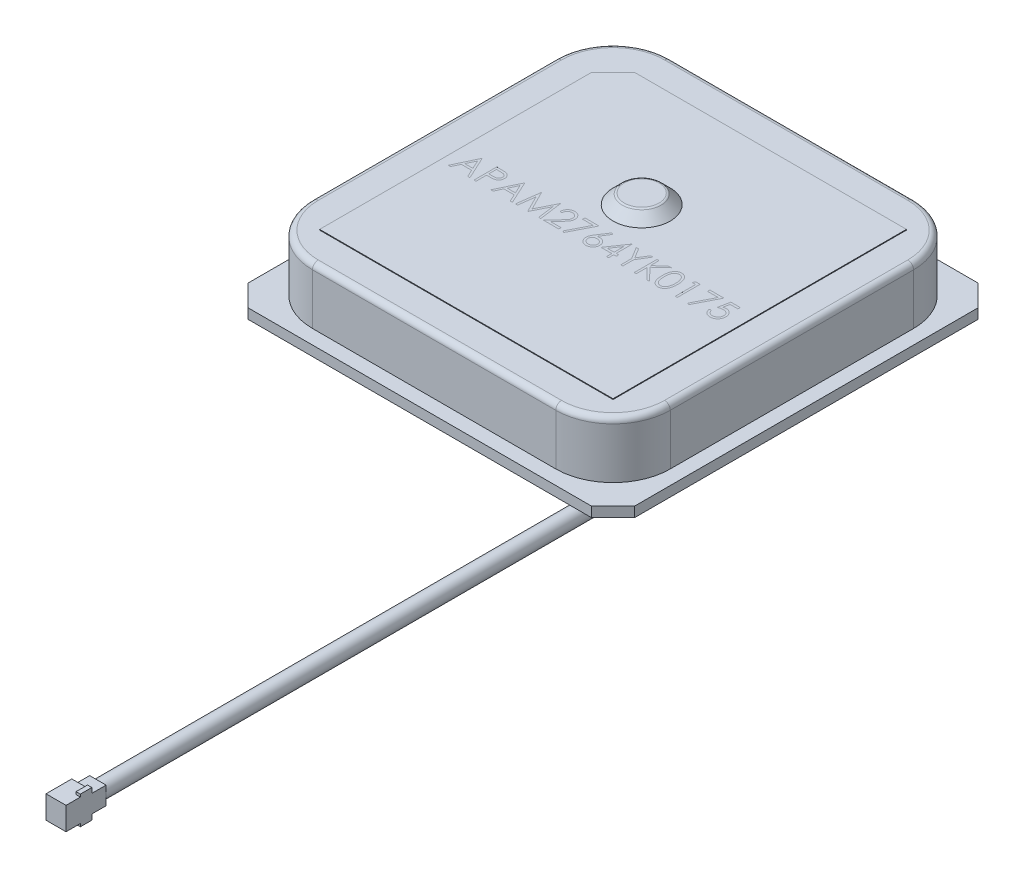
SolidWorks part; units mm, degrees
ref_plane "Front Plane" through (0, 0, 0) normal (0, 0, 1) x (1, 0, 0)
ref_plane "Top Plane" through (0, 0, 0) normal (0, 1, 0) x (1, 0, 0)
ref_plane "Right Plane" through (0, 0, 0) normal (1, 0, 0) x (0, 0, -1)
sketch "Sketch1" plane through (0, 0, 0) normal (0, 1, 0) x (1, 0, 0)
  line L0 (-13.5, -13.5) -> (13.5, -13.5)
  line L1 (-13.5, -13.5) -> (-13.5, 13.5)
  line L2 (13.5, -13.5) -> (13.5, 13.5)
  line L3 (-13.5, 13.5) -> (13.5, 13.5)
  line L4 (-13.5, -13.5) -> (13.5, 13.5) construction
  line L5 (13.5, -13.5) -> (-13.5, 13.5) construction
  point P1 (0, 0)
  dimension "D1" = 27
  dimension "D2" = 27
extrude "Boss-Extrude1" add sketch "Sketch1" along normal blind 0.7
chamfer "Chamfer2" distance 1.5 angle 45 4 edges at (-13.5, 0.35, 13.5) (13.5, 0.35, 13.5) (13.5, 0.35, -13.5) (-13.5, 0.35, -13.5)
sketch "Sketch2" plane through (0, 0.7, 0) normal (0, 1, 0) x (1, 0, 0)
  line L0 (-12.5, -12.5) -> (12.5, -12.5)
  line L1 (-12.5, -12.5) -> (-12.5, 12.5)
  line L2 (12.5, -12.5) -> (12.5, 12.5)
  line L3 (-12.5, 12.5) -> (12.5, 12.5)
  line L4 (-12.5, -12.5) -> (12.5, 12.5) construction
  line L5 (12.5, -12.5) -> (-12.5, 12.5) construction
  point P1 (0, 0)
  dimension "D1" = 25
  dimension "D2" = 25
extrude "Boss-Extrude3" add sketch "Sketch2" along normal blind 3.95 separate body
fillet "Fillet3" radius 4 4 edges at (12.5, 2.675, -12.5) (12.5, 2.675, 12.5) (-12.5, 2.675, 12.5) (-12.5, 2.675, -12.5)
sketch "Sketch3" plane through (0, 0, 0) normal (0, -1, 0) x (-1, 0, 0)
  line L0 (-11.5, -1.5) -> (3.5, -1.5)
  line L1 (-11.5, -1.5) -> (-11.5, 9.5)
  line L2 (3.5, -1.5) -> (3.5, 9.5)
  line L3 (-11.5, 9.5) -> (3.5, 9.5)
  line L5 (-13.5, -12) -> (-13.5, 12) construction
  line L6 (-12, 13.5) -> (12, 13.5) construction
  dimension "D1" = 15
  dimension "D2" = 11
  dimension "D3" = 15
  dimension "D4" = 17
fillet "Fillet4" radius 0.4 8 edges at (11.3284, 4.65, 11.3284) (0, 4.65, 12.5) (-11.3284, 4.65, 11.3284) (-12.5, 4.65, 0) (-11.3284, 4.65, -11.3284) (0, 4.65, -12.5) (11.3284, 4.65, -11.3284) (12.5, 4.65, 0)
sketch "Sketch5" plane through (0, 4.65, 0) normal (0, 1, 0) x (1, 0, 0)
  line L0 (-10.25, -10.25) -> (10.25, -10.25)
  line L1 (-10.25, -10.25) -> (-10.25, 10.25)
  line L2 (10.25, -10.25) -> (10.25, 10.25)
  line L3 (-10.25, 10.25) -> (10.25, 10.25)
  line L4 (-10.25, -10.25) -> (10.25, 10.25) construction
  line L5 (10.25, -10.25) -> (-10.25, 10.25) construction
  point P1 (0, 0)
  dimension "D1" = 20.5
  dimension "D2" = 20.5
extrude "Boss-Extrude6" add sketch "Sketch5" along normal blind 0.05
chamfer "Chamfer1" distance 1.5 angle 45 1 edges at (-10.25, 4.675, -10.25)
sketch "Sketch4" plane through (0, 4.7, 0) normal (0, 1, 0) x (1, 0, 0)
  line L1 (13.5, -12) -> (13.5, 12) construction
  line L2 (12, 13.5) -> (-12, 13.5) construction
  circle A0 centre (-0.5, 2.5) radius 2
  dimension "D1" = 4
  dimension "D2" = 14
  dimension "D3" = 11
extrude "Boss-Extrude5" add sketch "Sketch4" along normal blind 0.7 draft 45
fillet "Fillet1" radius 0.2 1 edges at (-0.5, 5.4, -1.2)
extrude "Boss-Extrude4" add sketch "Sketch3" along normal blind 1.3
sketch "Sketch6" plane through (0, 0, 1.5) normal (0, 0, 1) x (1, 0, 0)
  line L1 (11.5, -1.3) -> (11.5, 0) construction
  line L2 (14.85, 0) -> (-14.85, 0) construction
  circle A0 centre (10.7, -0.565) radius 0.565
  dimension "D3" = 1.13
  dimension "D2" = 0.8
extrude "Boss-Extrude10" add sketch "Sketch6" along normal blind 48 separate body
ref_plane "Plane1" through (11.28, 0, 0) normal (1, 0, 0) x (0, 0, -1)
sketch "Sketch7" plane through (11.28, 0, 0) normal (1, 0, 0) x (0, 0, -1)
  line L1 (-49.5, 0.235) -> (-47.7, 0.235)
  line L2 (-49.5, 0.235) -> (-49.5, -1.365)
  line L3 (-49.5, -1.365) -> (-47.7, -1.365)
  line L4 (-47.7, 0.235) -> (-47.7, -1.365)
  line L6 (-1.5, -0.565) -> (-17.1255, -0.565) construction
  line L7 (-1.5, -1.13) -> (-1.5, 0) construction
  line L8 (-49.5, 0) -> (-49.5, -1.13) construction
  dimension "D1" = 1.8
  dimension "D2" = 1.6
extrude "Boss-Extrude11" add sketch "Sketch7" against normal blind 1.4
sketch "Sketch8" plane through (11.28, 0, 0) normal (1, 0, 0) x (0, 0, -1)
  line L0 (-47.7, -1.365) -> (-47.7, 0.235) construction
  line L1 (-47.7, 0.06) -> (-46.7, 0.06)
  line L2 (-47.7, 0.06) -> (-47.7, -1.19)
  line L3 (-47.7, -1.19) -> (-46.7, -1.19)
  line L4 (-46.7, 0.06) -> (-46.7, -1.19)
  line L5 (-1.5, -0.565) -> (-49.5, -0.565) construction
  line L6 (-1.5, -1.13) -> (-1.5, 0) construction
  dimension "D1" = 1.25
  dimension "D2" = 1
extrude "Boss-Extrude12" add sketch "Sketch8" against normal blind 1.15
sketch "Sketch9" plane through (0, 0.235, 0) normal (0, 1, 0) x (1, 0, 0)
  line L1 (11.28, -47.7) -> (10.98, -47.7)
  line L2 (11.28, -47.7) -> (11.28, -48.5)
  line L3 (11.28, -48.5) -> (10.98, -48.5)
  line L4 (10.98, -47.7) -> (10.98, -48.5)
  dimension "D1" = 0.8
  dimension "D2" = 0.3
extrude "Boss-Extrude13" add sketch "Sketch9" against normal blind 1.8 and the other way blind 0.18
sketch "Sketch10" plane through (0, 4.7, 0) normal (0, 1, 0) x (1, 0, 0)
  text T0 " APAM2764YK0175" font "Century Gothic" height in points 6
extrude "Cut-Extrude1" cut sketch "Sketch10" against normal blind 0.0001
